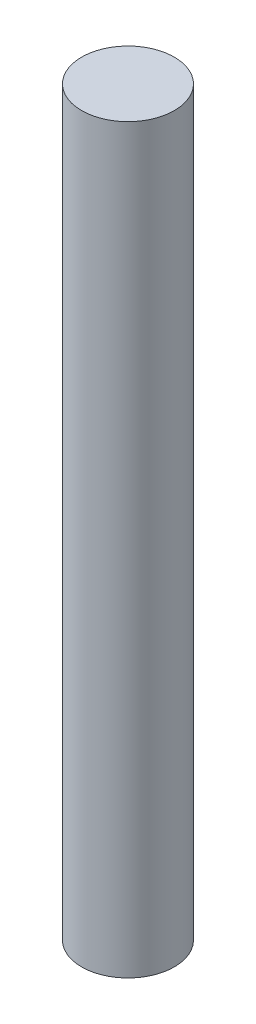
SolidWorks part; units mm, degrees
ref_plane "前视基准面" through (0, 0, 0) normal (0, 0, 1) x (1, 0, 0)
ref_plane "上视基准面" through (0, 0, 0) normal (0, 1, 0) x (1, 0, 0)
ref_plane "右视基准面" through (0, 0, 0) normal (1, 0, 0) x (0, 0, -1)
other "Configuration Table"
sketch "草图1" plane through (0, 0, 0) normal (0, 1, 0) x (1, 0, 0)
  circle A0 centre (0, 0) radius 1.5
  dimension "D1" = 3
extrude "凸台-拉伸1" add sketch "草图1" along normal blind 24
